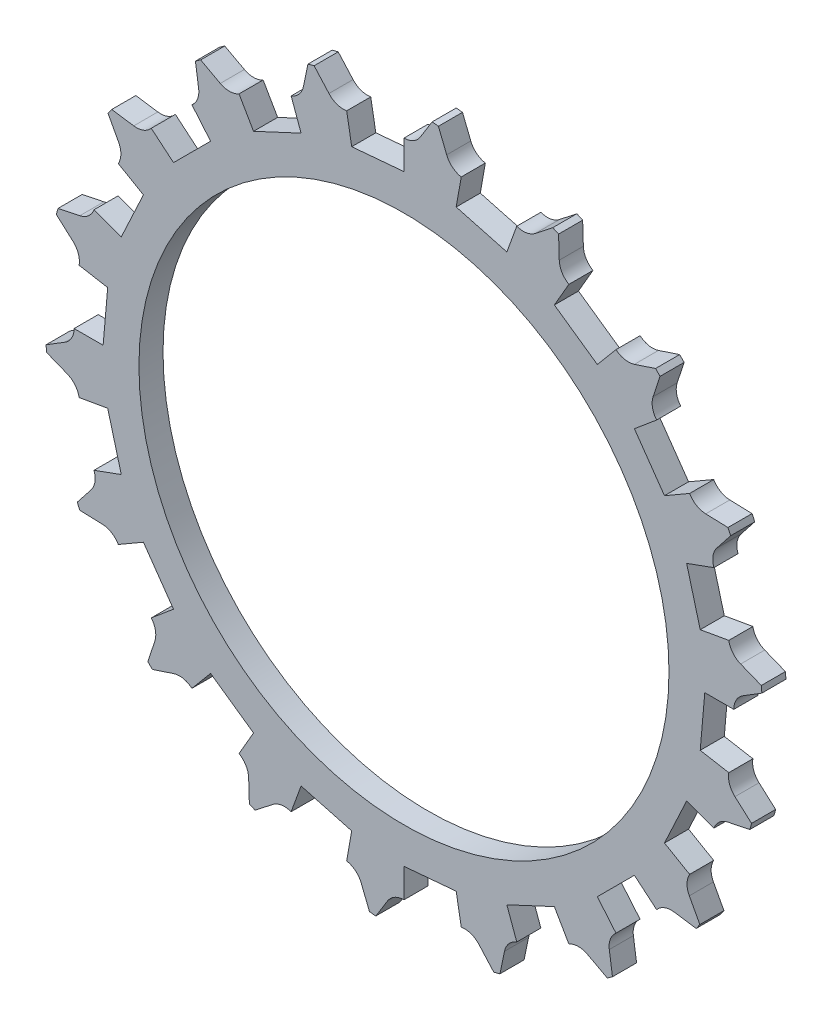
SolidWorks part; units mm, degrees
ref_plane "Front Plane" through (0, 0, 0) normal (0, 0, 1) x (1, 0, 0)
ref_plane "Top Plane" through (0, 0, 0) normal (0, 1, 0) x (1, 0, 0)
ref_plane "Right Plane" through (0, 0, 0) normal (1, 0, 0) x (0, 0, -1)
sketch "Sketch1" plane through (0, 0, 0) normal (0, 0, 1) x (1, 0, 0)
  line L0 (3.4006, 70.3439) -> (6.0855, 74.679)
  line L1 (3.4006, 70.3439) -> (8.8661, 69.8657) construction
  line L2 (6.9749, 74.6012) -> (8.8661, 69.8657)
  line L3 (3.4006, 70.3439) -> (0, 0) construction
  line L4 (0, 0) -> (8.8661, 69.8657) construction
  line L5 (15.5641, 68.6847) -> (18.9609, 72.4877)
  line L6 (19.8233, 72.2567) -> (20.8635, 67.2647)
  line L7 (27.2546, 64.9386) -> (31.2602, 68.094)
  line L8 (32.0693, 67.7166) -> (32.2269, 62.6199)
  line L9 (38.117, 59.2193) -> (42.6097, 61.6312)
  line L10 (43.341, 61.1191) -> (42.6111, 56.0725)
  line L11 (47.8212, 51.7007) -> (52.6645, 53.2958)
  line L12 (53.2958, 52.6645) -> (51.7007, 47.8212)
  line L13 (56.0725, 42.6111) -> (61.1191, 43.341)
  line L14 (61.6312, 42.6097) -> (59.2193, 38.117)
  line L15 (62.6199, 32.2269) -> (67.7166, 32.0693)
  line L16 (68.094, 31.2602) -> (64.9386, 27.2546)
  line L17 (67.2647, 20.8635) -> (72.2567, 19.8233)
  line L18 (72.4877, 18.9609) -> (68.6847, 15.5641)
  line L19 (69.8657, 8.8661) -> (74.6012, 6.9749)
  line L20 (74.679, 6.0855) -> (70.3439, 3.4006)
  line L21 (70.3439, -3.4006) -> (74.679, -6.0855)
  line L22 (74.6012, -6.9749) -> (69.8657, -8.8661)
  line L23 (68.6847, -15.5641) -> (72.4877, -18.9609)
  line L24 (72.2567, -19.8233) -> (67.2647, -20.8635)
  line L25 (64.9386, -27.2546) -> (68.094, -31.2602)
  line L26 (67.7166, -32.0693) -> (62.6199, -32.2269)
  line L27 (59.2193, -38.117) -> (61.6312, -42.6097)
  line L28 (61.1191, -43.341) -> (56.0725, -42.6111)
  line L29 (51.7007, -47.8212) -> (53.2958, -52.6645)
  line L30 (52.6645, -53.2958) -> (47.8212, -51.7007)
  line L31 (42.6111, -56.0725) -> (43.341, -61.1191)
  line L32 (42.6097, -61.6312) -> (38.117, -59.2193)
  line L33 (32.2269, -62.6199) -> (32.0693, -67.7166)
  line L34 (31.2602, -68.094) -> (27.2546, -64.9386)
  line L35 (20.8635, -67.2647) -> (19.8233, -72.2567)
  line L36 (18.9609, -72.4877) -> (15.5641, -68.6847)
  line L37 (8.8661, -69.8657) -> (6.9749, -74.6012)
  line L38 (6.0855, -74.679) -> (3.4006, -70.3439)
  line L39 (-3.4006, -70.3439) -> (-6.0855, -74.679)
  line L40 (-6.9749, -74.6012) -> (-8.8661, -69.8657)
  line L41 (-15.5641, -68.6847) -> (-18.9609, -72.4877)
  line L42 (-19.8233, -72.2567) -> (-20.8635, -67.2647)
  line L43 (-27.2546, -64.9386) -> (-31.2602, -68.094)
  line L44 (-32.0693, -67.7166) -> (-32.2269, -62.6199)
  line L45 (-38.117, -59.2193) -> (-42.6097, -61.6312)
  line L46 (-43.341, -61.1191) -> (-42.6111, -56.0725)
  line L47 (-47.8212, -51.7007) -> (-52.6645, -53.2958)
  line L48 (-53.2958, -52.6645) -> (-51.7007, -47.8212)
  line L49 (-56.0725, -42.6111) -> (-61.1191, -43.341)
  line L50 (-61.6312, -42.6097) -> (-59.2193, -38.117)
  line L51 (-62.6199, -32.2269) -> (-67.7166, -32.0693)
  line L52 (-68.094, -31.2602) -> (-64.9386, -27.2546)
  line L53 (-67.2647, -20.8635) -> (-72.2567, -19.8233)
  line L54 (-72.4877, -18.9609) -> (-68.6847, -15.5641)
  line L55 (-69.8657, -8.8661) -> (-74.6012, -6.9749)
  line L56 (-74.679, -6.0855) -> (-70.3439, -3.4006)
  line L57 (-70.3439, 3.4006) -> (-74.679, 6.0855)
  line L58 (-74.6012, 6.9749) -> (-69.8657, 8.8661)
  line L59 (-68.6847, 15.5641) -> (-72.4877, 18.9609)
  line L60 (-72.2567, 19.8233) -> (-67.2647, 20.8635)
  line L61 (-64.9386, 27.2546) -> (-68.094, 31.2602)
  line L62 (-67.7166, 32.0693) -> (-62.6199, 32.2269)
  line L63 (-59.2193, 38.117) -> (-61.6312, 42.6097)
  line L64 (-61.1191, 43.341) -> (-56.0725, 42.6111)
  line L65 (-51.7007, 47.8212) -> (-53.2958, 52.6645)
  line L66 (-52.6645, 53.2958) -> (-47.8212, 51.7007)
  line L67 (-42.6111, 56.0725) -> (-43.341, 61.1191)
  line L68 (-42.6097, 61.6312) -> (-38.117, 59.2193)
  line L69 (-32.2269, 62.6199) -> (-32.0693, 67.7166)
  line L70 (-31.2602, 68.094) -> (-27.2546, 64.9386)
  line L71 (-20.8635, 67.2647) -> (-19.8233, 72.2567)
  line L72 (-18.9609, 72.4877) -> (-15.5641, 68.6847)
  line L73 (-8.8661, 69.8657) -> (-6.9749, 74.6012)
  line L74 (-6.0855, 74.679) -> (-3.4006, 70.3439)
  line L83 (0, 72.45) -> (0, 0) construction
  line L84 (0, 0) -> (6.5105, 74.4157) construction
  circle A0 centre (0, 0) radius 72.45 construction
  arc A1 (-3.9985, 72.3396) -> (3.4006, 70.3439) centre (0, 72.45) ccw
  arc A2 (4.6139, 72.3029) -> (8.0115, 72.0057) centre (0, 0) cw
  arc A3 (6.0855, 74.679) -> (6.9749, 74.6012) centre (6.5105, 74.4157) cw
  arc A4 (8.6239, 71.9349) -> (15.5641, 68.6847) centre (12.5808, 71.3493) ccw
  arc A5 (18.9609, 72.4877) -> (19.8233, 72.2567) centre (19.3338, 72.1547) cw
  arc A6 (20.9843, 69.3445) -> (27.2546, 64.9386) centre (24.7794, 68.0807) ccw
  arc A7 (31.2602, 68.094) -> (32.0693, 67.7166) centre (31.5696, 67.7012) cw
  arc A8 (32.707, 64.6472) -> (38.117, 59.2193) centre (36.225, 62.7435) ccw
  arc A9 (42.6097, 61.6312) -> (43.341, 61.1191) centre (42.8462, 61.1907) cw
  arc A10 (43.436, 57.9855) -> (47.8212, 51.7007) centre (46.57, 55.4999) ccw
  arc A11 (52.6645, 53.2958) -> (53.2958, 52.6645) centre (52.8209, 52.8209) cw
  arc A12 (52.8452, 49.562) -> (56.0725, 42.6111) centre (55.4999, 46.57) ccw
  arc A13 (61.1191, 43.341) -> (61.6312, 42.6097) centre (61.1907, 42.8462) cw
  arc A14 (60.6487, 39.6326) -> (62.6199, 32.2269) centre (62.7435, 36.225) ccw
  arc A15 (67.7166, 32.0693) -> (68.094, 31.2602) centre (67.7012, 31.5696) cw
  arc A16 (66.6094, 28.4989) -> (67.2647, 20.8635) centre (68.0807, 24.7794) ccw
  arc A17 (72.2567, 19.8233) -> (72.4877, 18.9609) centre (72.1547, 19.3338) cw
  arc A18 (70.5463, 16.4994) -> (69.8657, 8.8661) centre (71.3493, 12.5808) ccw
  arc A19 (74.6012, 6.9749) -> (74.679, 6.0855) centre (74.4157, 6.5105) cw
  arc A20 (72.3396, 3.9985) -> (70.3439, -3.4006) centre (72.45, 0) ccw
  arc A21 (74.679, -6.0855) -> (74.6012, -6.9749) centre (74.4157, -6.5105) cw
  arc A22 (71.9349, -8.6239) -> (68.6847, -15.5641) centre (71.3493, -12.5808) ccw
  arc A23 (72.4877, -18.9609) -> (72.2567, -19.8233) centre (72.1547, -19.3338) cw
  arc A24 (69.3445, -20.9843) -> (64.9386, -27.2546) centre (68.0807, -24.7794) ccw
  arc A25 (68.094, -31.2602) -> (67.7166, -32.0693) centre (67.7012, -31.5696) cw
  arc A26 (64.6472, -32.707) -> (59.2193, -38.117) centre (62.7435, -36.225) ccw
  arc A27 (61.6312, -42.6097) -> (61.1191, -43.341) centre (61.1907, -42.8462) cw
  arc A28 (57.9855, -43.436) -> (51.7007, -47.8212) centre (55.4999, -46.57) ccw
  arc A29 (53.2958, -52.6645) -> (52.6645, -53.2958) centre (52.8209, -52.8209) cw
  arc A30 (49.562, -52.8452) -> (42.6111, -56.0725) centre (46.57, -55.4999) ccw
  arc A31 (43.341, -61.1191) -> (42.6097, -61.6312) centre (42.8462, -61.1907) cw
  arc A32 (39.6326, -60.6487) -> (32.2269, -62.6199) centre (36.225, -62.7435) ccw
  arc A33 (32.0693, -67.7166) -> (31.2602, -68.094) centre (31.5696, -67.7012) cw
  arc A34 (28.4989, -66.6094) -> (20.8635, -67.2647) centre (24.7794, -68.0807) ccw
  arc A35 (19.8233, -72.2567) -> (18.9609, -72.4877) centre (19.3338, -72.1547) cw
  arc A36 (16.4994, -70.5463) -> (8.8661, -69.8657) centre (12.5808, -71.3493) ccw
  arc A37 (6.9749, -74.6012) -> (6.0855, -74.679) centre (6.5105, -74.4157) cw
  arc A38 (3.9985, -72.3396) -> (-3.4006, -70.3439) centre (0, -72.45) ccw
  arc A39 (-6.0855, -74.679) -> (-6.9749, -74.6012) centre (-6.5105, -74.4157) cw
  arc A40 (-8.6239, -71.9349) -> (-15.5641, -68.6847) centre (-12.5808, -71.3493) ccw
  arc A41 (-18.9609, -72.4877) -> (-19.8233, -72.2567) centre (-19.3338, -72.1547) cw
  arc A42 (-20.9843, -69.3445) -> (-27.2546, -64.9386) centre (-24.7794, -68.0807) ccw
  arc A43 (-31.2602, -68.094) -> (-32.0693, -67.7166) centre (-31.5696, -67.7012) cw
  arc A44 (-32.707, -64.6472) -> (-38.117, -59.2193) centre (-36.225, -62.7435) ccw
  arc A45 (-42.6097, -61.6312) -> (-43.341, -61.1191) centre (-42.8462, -61.1907) cw
  arc A46 (-43.436, -57.9855) -> (-47.8212, -51.7007) centre (-46.57, -55.4999) ccw
  arc A47 (-52.6645, -53.2958) -> (-53.2958, -52.6645) centre (-52.8209, -52.8209) cw
  arc A48 (-52.8452, -49.562) -> (-56.0725, -42.6111) centre (-55.4999, -46.57) ccw
  arc A49 (-61.1191, -43.341) -> (-61.6312, -42.6097) centre (-61.1907, -42.8462) cw
  arc A50 (-60.6487, -39.6326) -> (-62.6199, -32.2269) centre (-62.7435, -36.225) ccw
  arc A51 (-67.7166, -32.0693) -> (-68.094, -31.2602) centre (-67.7012, -31.5696) cw
  arc A52 (-66.6094, -28.4989) -> (-67.2647, -20.8635) centre (-68.0807, -24.7794) ccw
  arc A53 (-72.2567, -19.8233) -> (-72.4877, -18.9609) centre (-72.1547, -19.3338) cw
  arc A54 (-70.5463, -16.4994) -> (-69.8657, -8.8661) centre (-71.3493, -12.5808) ccw
  arc A55 (-74.6012, -6.9749) -> (-74.679, -6.0855) centre (-74.4157, -6.5105) cw
  arc A56 (-72.3396, -3.9985) -> (-70.3439, 3.4006) centre (-72.45, 0) ccw
  arc A57 (-74.679, 6.0855) -> (-74.6012, 6.9749) centre (-74.4157, 6.5105) cw
  arc A58 (-71.9349, 8.6239) -> (-68.6847, 15.5641) centre (-71.3493, 12.5808) ccw
  arc A59 (-72.4877, 18.9609) -> (-72.2567, 19.8233) centre (-72.1547, 19.3338) cw
  arc A60 (-69.3445, 20.9843) -> (-64.9386, 27.2546) centre (-68.0807, 24.7794) ccw
  arc A61 (-68.094, 31.2602) -> (-67.7166, 32.0693) centre (-67.7012, 31.5696) cw
  arc A62 (-64.6472, 32.707) -> (-59.2193, 38.117) centre (-62.7435, 36.225) ccw
  arc A63 (-61.6312, 42.6097) -> (-61.1191, 43.341) centre (-61.1907, 42.8462) cw
  arc A64 (-57.9855, 43.436) -> (-51.7007, 47.8212) centre (-55.4999, 46.57) ccw
  arc A65 (-53.2958, 52.6645) -> (-52.6645, 53.2958) centre (-52.8209, 52.8209) cw
  arc A66 (-49.562, 52.8452) -> (-42.6111, 56.0725) centre (-46.57, 55.4999) ccw
  arc A67 (-43.341, 61.1191) -> (-42.6097, 61.6312) centre (-42.8462, 61.1907) cw
  arc A68 (-39.6326, 60.6487) -> (-32.2269, 62.6199) centre (-36.225, 62.7435) ccw
  arc A69 (-32.0693, 67.7166) -> (-31.2602, 68.094) centre (-31.5696, 67.7012) cw
  arc A70 (-28.4989, 66.6094) -> (-20.8635, 67.2647) centre (-24.7794, 68.0807) ccw
  arc A71 (-19.8233, 72.2567) -> (-18.9609, 72.4877) centre (-19.3338, 72.1547) cw
  arc A72 (-16.4994, 70.5463) -> (-8.8661, 69.8657) centre (-12.5808, 71.3493) ccw
  arc A73 (-6.9749, 74.6012) -> (-6.0855, 74.679) centre (-6.5105, 74.4157) cw
  point P289 (0, 0)
  dimension "D1" = 144.9
  dimension "D2" = 4
  dimension "D5" = 0.5
  dimension "D6" = 74.7
  dimension "D3" = 5
  dimension "D4" = 36
extrude "Boss-Extrude1" add sketch "Sketch1" along normal blind 5
sketch "Sketch2" plane through (0, 0, 5) normal (0, 0, 1) x (1, 0, 0)
  circle A0 centre (0, 0) radius 12.5
  dimension "D1" = 25
extrude "Boss-Extrude2" add sketch "Sketch2" along normal blind 40
sketch "Sketch5" plane through (0, 0, 0) normal (0, 0, -1) x (-1, 0, 0)
  line L1 (0, 68.45) -> (0.611, 75.4338)
  line L2 (11.8862, 67.4101) -> (12.4972, 74.3939)
  line L3 (0.611, 75.4338) -> (12.4972, 74.3939)
  line L4 (0, 68.45) -> (0, 62.4271)
  line L5 (0, 62.4271) -> (10.8403, 61.4787)
  line L6 (10.8403, 61.4787) -> (11.8862, 67.4101)
  arc A0 (0, 68.45) -> (11.8862, 67.4101) centre (6.4077, 73.2398) ccw
  arc A3 (-3.4006, 70.3439) -> (3.4006, 70.3439) centre (0, 72.45) ccw construction
  arc A5 (-3.4006, 70.3439) -> (3.4006, 70.3439) centre (0, 72.45) ccw construction
  arc A7 (8.8661, 69.8657) -> (15.5641, 68.6847) centre (12.5808, 71.3493) ccw construction
  arc A8 (6.9749, 74.6012) -> (6.0855, 74.679) centre (6.5105, 74.4157) ccw construction
  point P0 (13.9801, 53.8761)
  point P19 (0, 68.45)
  point P22 (11.8862, 67.4101)
  dimension "D4" = 8
  dimension "D1" = 6
extrude "Cut-Extrude2" cut sketch "Sketch5" against normal blind 10 contours A0 L4 L5 L6 | L1 A0 L2 L3
sketch "Sketch9" plane through (0, 0, 0) normal (0, 0, -1) x (-1, 0, 0)
  circle A0 centre (0, 0) radius 74.5
  circle A1 centre (0, 0) radius 100
  dimension "D1" = 149
  dimension "D2" = 200
extrude "Cut-Extrude5" cut sketch "Sketch9" against normal blind 10
fillet "Fillet1" radius 30 1 edges at (12.5, 0, 5)
sketch "Sketch3" plane through (0, 0, 45) normal (0, 0, 1) x (1, 0, 0)
  circle A0 centre (0, 0) radius 5
  dimension "D1" = 10
extrude "Cut-Extrude1" cut sketch "Sketch3" against normal through all
hole_wizard "Ø1.0mm Dowel Hole1" positions "3DSketch1" profile "Sketch4" hole size "Ø1.0" standard "ANSI Metric"
sketch3d "3DSketch1"
  point P0 (-6.8176, -10.4771, 42.0201)
  point P2 (-11.0684, 5.8086, 41.6583)
sketch "Sketch4" plane through (-6.8176, -10.4771, 42.0201) normal (0, 0, 1) x (0.8382, -0.5454, 0)
  line L0 (0, 0) -> (0, 34)
  line L1 (0, 34) -> (1.4, 33.1588)
  line L2 (1.4, 33.1588) -> (1.4, 0)
  line L5 (1.4, 0) -> (0, 0)
  line L10 (0, 34) -> (-1.4, 33.1588) construction
  line L11 (0, -6.35) -> (0, 107.95) construction
  dimension "Hole Dia." = 2.8
  dimension "Hole Depth" = 34
  dimension "Drill Angle" = 118
pattern_circular "CirPattern1" count 18 over 360 about axis through (0, 0, 0) along (0, 0, 1) of "Cut-Extrude2"
sketch "Sketch6" plane through (0, 0, 0) normal (0, 1, 0) x (1, 0, 0)
  line L0 (-71.7872, -5) -> (-67.2647, -5) construction
  line L1 (-74.2713, -5) -> (79.9055, -5)
  line L2 (-74.2713, -5) -> (-74.2713, -50.9165)
  line L3 (-74.2713, -50.9165) -> (79.9055, -50.9165)
  line L4 (79.9055, -5) -> (79.9055, -50.9165)
extrude "Cut-Extrude3" cut sketch "Sketch6" against normal through all both and the other way through all
sketch "Sketch7" plane through (0, 0, 0) normal (0, 0, -1) x (-1, 0, 0)
  line L1 (12.6, -7.2746) -> (12.6, 7.2746)
  line L2 (12.6, 7.2746) -> (0, 14.5492)
  line L3 (0, 14.5492) -> (-12.6, 7.2746)
  line L4 (-12.6, 7.2746) -> (-12.6, -7.2746)
  line L5 (-12.6, -7.2746) -> (0, -14.5492)
  line L6 (0, -14.5492) -> (12.6, -7.2746)
  circle A0 centre (0, 0) radius 12.6 construction
  dimension "D1" = 25.2
extrude "Cut-Extrude4" cut sketch "Sketch7" against normal through all both
sketch "Sketch10" plane through (0, 0, 0) normal (0, 0, -1) x (-1, 0, 0)
  circle A0 centre (0, 0) radius 55
  dimension "D1" = 110
extrude "Cut-Extrude6" cut sketch "Sketch10" against normal blind 10
equation "\"Teeth\"= 36"
equation "\"D4@Sketch1\"=\"Teeth\""
equation "\"D6@Sketch1\"=83/40*\"Teeth\""
equation "\"D1@Sketch1\"=161/40*\"Teeth\""
equation "\"D3@Sketch1\"=4.5/\"Teeth\"*40"
equation "\"D1@CirPattern1\"=\"Teeth\"/2"
